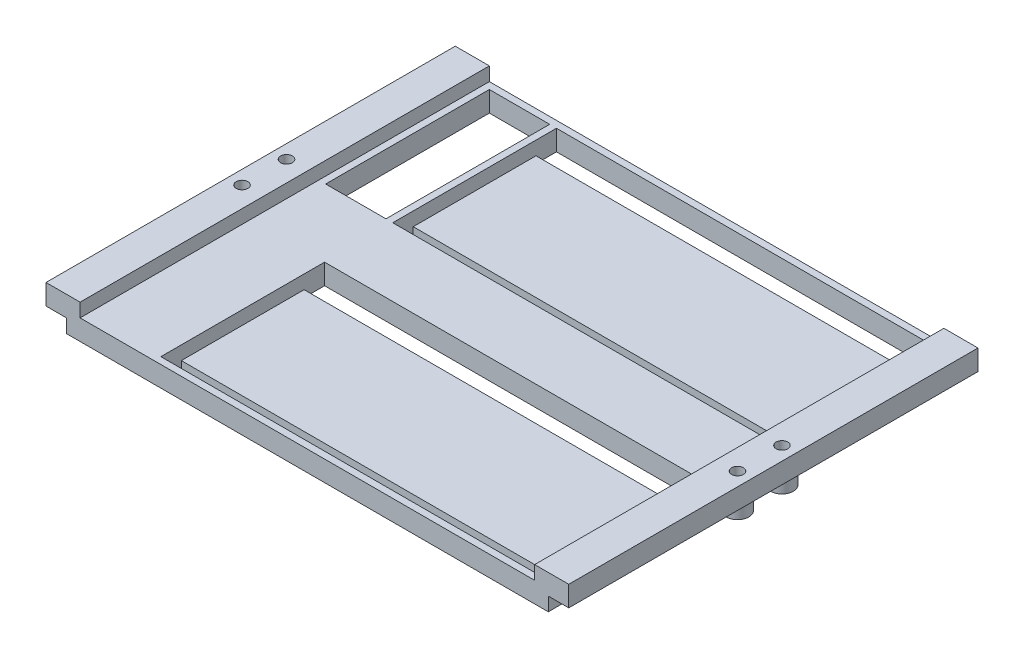
SolidWorks part; units mm, degrees
ref_plane "Front Plane" through (0, 0, 0) normal (0, 0, 1) x (1, 0, 0)
ref_plane "Top Plane" through (0, 0, 0) normal (0, 1, 0) x (1, 0, 0)
ref_plane "Right Plane" through (0, 0, 0) normal (1, 0, 0) x (0, 0, -1)
sketch "Sketch2" plane through (0, 0, 0) normal (0, 0, 1) x (1, 0, 0)
  line L0 (179.1, 12.5) -> (191.6, 12.5)
  line L1 (7.5, 0) -> (184.1, 0)
  line L2 (0, 5) -> (0, 12.5)
  line L3 (0, 12.5) -> (12.5, 12.5)
  line L4 (191.6, 5) -> (191.6, 12.5)
  line L7 (0, 5) -> (7.5, 5)
  line L8 (7.5, 0) -> (7.5, 5)
  line L11 (191.6, 5) -> (184.1, 5)
  line L12 (184.1, 0) -> (184.1, 5)
  line L14 (12.5, 12.5) -> (12.5, 7.5)
  line L15 (12.5, 7.5) -> (179.1, 7.5)
  line L16 (179.1, 12.5) -> (179.1, 7.5)
  dimension "D1" = 191.6
  dimension "D2" = 5
  dimension "D3" = 5
  dimension "D4" = 5
  dimension "D5" = 12.5
  dimension "D6" = 7.5
  dimension "D7" = 7.5
  dimension "D8" = 12.5
  dimension "D9" = 12.5
extrude "PlateFrame" add sketch "Sketch2" along normal blind 150
sketch "Sketch3" plane through (0, 12.5, 0) normal (0, 1, 0) x (1, 0, 0)
  line L0 (12.5, 0) -> (0, 0) construction
  line L2 (0, -150) -> (0, 0) construction
  line L3 (191.6, -150) -> (191.6, 0) construction
  line L4 (191.6, 0) -> (179.1, 0) construction
  circle A0 centre (5, -66.85) radius 2.15
  circle A1 centre (5, -83.15) radius 2.15
  circle A2 centre (186.6, -66.85) radius 2.15
  circle A3 centre (186.6, -83.15) radius 2.15
  dimension "D1" = 4.3
  dimension "D2" = 4.3
  dimension "D3" = 4.3
  dimension "D4" = 4.3
  dimension "D5" = 66.85
  dimension "D6" = 16.3
  dimension "D7" = 5
  dimension "D8" = 5
  dimension "D9" = 5
  dimension "D10" = 181.6
  dimension "D11" = 66.85
  dimension "D12" = 16.3
extrude "HoleSupport" cut sketch "Sketch3" against normal blind 7.5
sketch "Sketch4" plane through (0, 12.5, 0) normal (0, 1, 0) x (1, 0, 0)
  circle A0 centre (5, -66.85) radius 2.15
  circle A1 centre (5, -83.15) radius 2.15
  circle A2 centre (186.6, -83.15) radius 2.15
  circle A3 centre (186.6, -66.85) radius 2.15
  circle A4 centre (186.6, -66.85) radius 4.15
  circle A5 centre (186.6, -83.15) radius 4.15
  circle A6 centre (5, -66.85) radius 4.15
  circle A7 centre (5, -83.15) radius 4.15
  dimension "D1" = 2
extrude "CylindricalSupports" add sketch "Sketch4" against normal blind 12.5
sketch "Sketch8" plane through (0, 7.5, 0) normal (0, 1, 0) x (1, 0, 0)
  line L1 (179.1, -150) -> (179.1, 0) construction
  line L2 (176.6, -2.5) -> (39.6, -2.5)
  line L3 (176.6, -2.5) -> (176.6, -62.5)
  line L4 (176.6, -62.5) -> (39.6, -62.5)
  line L5 (39.6, -2.5) -> (39.6, -62.5)
  line L6 (176.6, -147.5) -> (39.6, -147.5)
  line L7 (176.6, -147.5) -> (176.6, -87.5)
  line L8 (176.6, -87.5) -> (39.6, -87.5)
  line L9 (39.6, -147.5) -> (39.6, -87.5)
  line L10 (179.1, 0) -> (12.5, 0) construction
  line L11 (179.1, -150) -> (12.5, -150) construction
  line L12 (179.1, -150) -> (179.1, 0) construction
  dimension "D1" = 2.5
  dimension "D2" = 2.5
  dimension "D3" = 2.5
  dimension "D4" = 2.5
  dimension "D5" = 60
  dimension "D6" = 60
  dimension "D7" = 137
  dimension "D8" = 137
extrude "ItemLayout" cut sketch "Sketch8" against normal blind 5
sketch "Sketch9" plane through (0, 2.5, 0) normal (0, 1, 0) x (1, 0, 0)
  line L0 (176.6, -147.5) -> (176.6, -87.5) construction
  line L1 (39.6, -147.5) -> (176.6, -147.5)
  line L2 (39.6, -147.5) -> (39.6, -140)
  line L3 (39.6, -140) -> (176.6, -140)
  line L4 (176.6, -147.5) -> (176.6, -140)
  line L5 (39.6, -2.5) -> (39.6, -62.5) construction
  line L6 (176.6, -2.5) -> (39.6, -2.5)
  line L7 (176.6, -2.5) -> (176.6, -10)
  line L8 (176.6, -10) -> (39.6, -10)
  line L9 (39.6, -2.5) -> (39.6, -10)
  line L10 (176.6, -147.5) -> (176.6, -87.5) construction
  line L11 (39.6, -87.5) -> (176.6, -87.5)
  line L12 (39.6, -87.5) -> (39.6, -95)
  line L13 (39.6, -95) -> (176.6, -95)
  line L14 (176.6, -87.5) -> (176.6, -95)
  line L15 (39.6, -2.5) -> (39.6, -62.5) construction
  line L16 (176.6, -62.5) -> (39.6, -62.5)
  line L17 (176.6, -62.5) -> (176.6, -55)
  line L18 (176.6, -55) -> (39.6, -55)
  line L19 (39.6, -62.5) -> (39.6, -55)
  dimension "D1" = 7.5
  dimension "D2" = 7.5
  dimension "D3" = 7.5
  dimension "D4" = 7.5
extrude "VelcroHoles" cut sketch "Sketch9" against normal through all
sketch "Sketch10" plane through (0, 7.5, 0) normal (0, 1, 0) x (1, 0, 0)
  line L0 (179.1, 0) -> (12.5, 0) construction
  line L1 (15, -2.5) -> (37.1, -2.5)
  line L2 (15, -2.5) -> (15, -62.5)
  line L3 (15, -62.5) -> (37.1, -62.5)
  line L4 (37.1, -2.5) -> (37.1, -62.5)
  line L5 (12.5, -150) -> (12.5, 0) construction
  line L6 (39.6, -2.5) -> (39.6, -62.5) construction
  dimension "D1" = 2.5
  dimension "D2" = 2.5
  dimension "D3" = 2.5
  dimension "D4" = 60
extrude "OpenHole" cut sketch "Sketch10" against normal through all
